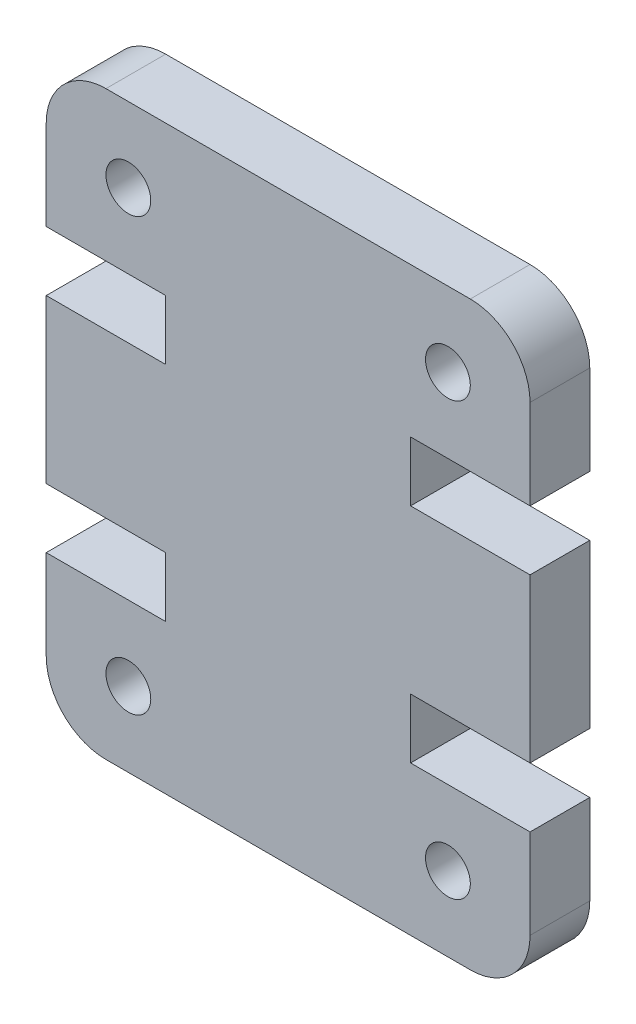
SolidWorks part; units mm, degrees
ref_plane "Front Plane" through (0, 0, 0) normal (0, 0, 1) x (1, 0, 0)
ref_plane "Top Plane" through (0, 0, 0) normal (0, 1, 0) x (1, 0, 0)
ref_plane "Right Plane" through (0, 0, 0) normal (1, 0, 0) x (0, 0, -1)
sketch "Sketch2" plane through (0, 0, 0) normal (0, 0, 1) x (1, 0, 0)
  line L0 (0, 7) -> (0, 12.455)
  line L1 (2, 0) -> (14.2, 0)
  line L2 (16.2, 5) -> (16.2, 2)
  line L3 (0, 9.7275) -> (16.2, 9.7275) construction
  line L4 (12.2, 5) -> (16.2, 5)
  line L5 (16.2, 7) -> (12.2, 7)
  line L6 (12.2, 7) -> (12.2, 5)
  line L7 (16.2, 7) -> (16.2, 12.455)
  line L8 (4, 7) -> (4, 5)
  line L9 (0, 14.455) -> (0, 17.455)
  line L10 (0, 7) -> (4, 7)
  line L11 (4, 5) -> (0, 5)
  line L12 (4, 14.455) -> (0, 14.455)
  line L13 (0, 12.455) -> (4, 12.455)
  line L14 (4, 12.455) -> (4, 14.455)
  line L15 (12.2, 12.455) -> (12.2, 14.455)
  line L16 (16.2, 12.455) -> (12.2, 12.455)
  line L17 (12.2, 14.455) -> (16.2, 14.455)
  line L18 (16.2, 14.455) -> (16.2, 17.455)
  line L19 (0, 5) -> (0, 2)
  line L20 (8.1, 19.455) -> (8.1, 0) construction
  line L21 (2, 19.455) -> (14.2, 19.455)
  circle A0 centre (13.45, 2.5) radius 0.75
  arc A1 (16.2, 2) -> (14.2, 0) centre (14.2, 2) cw
  circle A2 centre (2.75, 16.955) radius 0.75
  arc A3 (0, 2) -> (2, 0) centre (2, 2) ccw
  arc A4 (0, 17.455) -> (2, 19.455) centre (2, 17.455) cw
  circle A5 centre (2.75, 2.5) radius 0.75
  arc A6 (16.2, 17.455) -> (14.2, 19.455) centre (14.2, 17.455) ccw
  circle A7 centre (13.45, 16.955) radius 0.75
  point P18 (8.1, 9.7275)
  dimension "D1" = 1.5
  dimension "D2" = 2
  dimension "D3" = 2.75
  dimension "D4" = 8.1
  dimension "D5" = 2.5
  dimension "D6" = 5
  dimension "D8" = 9.7275
extrude "Boss-Extrude1" add sketch "Sketch2" along normal blind 2
equation "\"D4@Sketch2\"= \"fingerWidth@parametersSketch@prostheticParameters.SLDPRT\" / 2'Finger Width"
equation "\"D8@Sketch2\"= ( ( \"HL@parametersSketch@prostheticParameters.SLDPRT\" * 0.143 ) - 3 - 4 ) / 2 'MIP Length -SiliconeDIP-SiliconeMIP"
